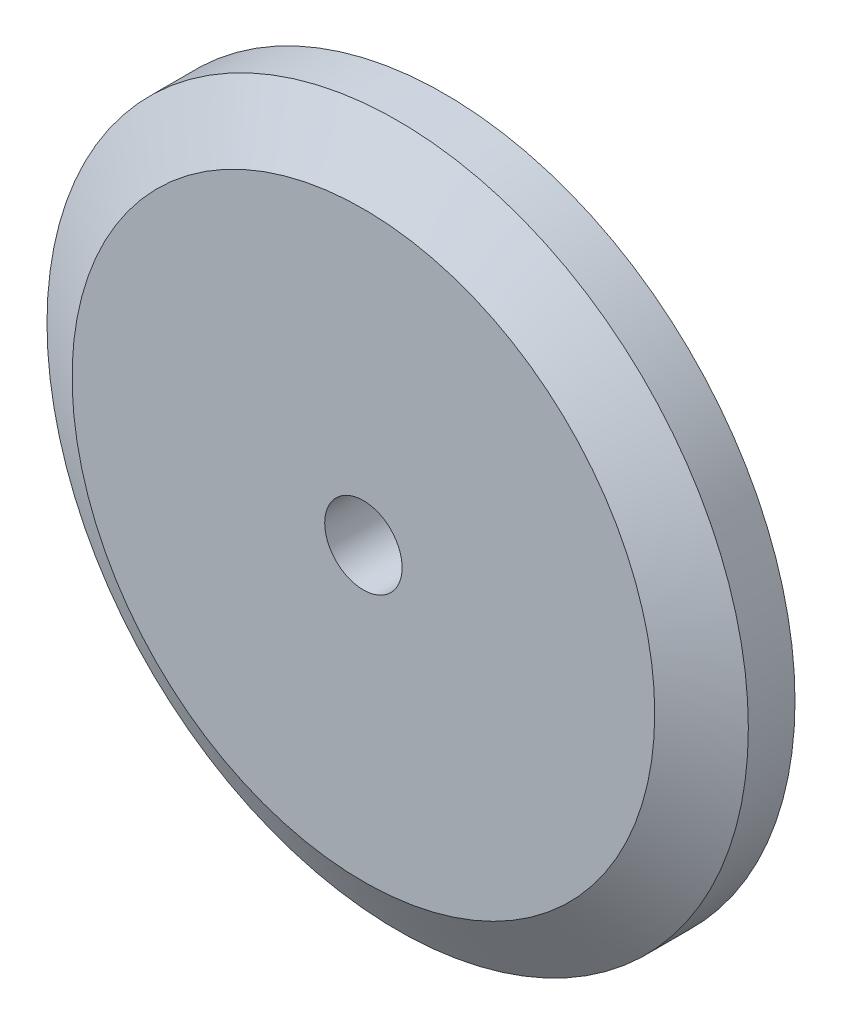
SolidWorks part; units mm, degrees
ref_plane "Front Plane" through (0, 0, 0) normal (0, 0, 1) x (1, 0, 0)
ref_plane "Top Plane" through (0, 0, 0) normal (0, 1, 0) x (1, 0, 0)
ref_plane "Right Plane" through (0, 0, 0) normal (1, 0, 0) x (0, 0, -1)
sketch "Sketch2" plane through (0, 0, -0.5) normal (0, 0, 1) x (1, 0, 0)
  circle A0 centre (40.4, -23.75) radius 5.5
  circle A1 centre (40.4, -23.75) radius 3.873 construction
  circle A2 centre (40.4, -23.75) radius 3.873 construction
  circle A3 centre (40.4, -23.75) radius 3.923
  circle A4 centre (40.4, -23.75) radius 5.5 construction
  dimension "D1" = 0.05
extrude "Boss-Extrude1" add sketch "Sketch2" along normal blind 0.5
sketch "Sketch3" plane through (0, 0, 0) normal (0, 0, 1) x (1, 0, 0)
  circle A0 centre (40.4, -23.75) radius 13
  circle A1 centre (40.4, -23.75) radius 13 construction
  circle A2 centre (40.4, -23.75) radius 3.923 construction
  circle A3 centre (40.4, -23.75) radius 3.923
  circle M1 centre (40.4, -23.75) radius 5.5
  circle M2 centre (40.4, -23.75) radius 3.923
extrude "Boss-Extrude2" add sketch "Sketch3" along normal blind 3 contours A0 M1 | M2 | M1 M2
sketch "Sketch4" plane through (0, 0, 0) normal (0, 0, -1) x (-1, 0, 0)
  circle A0 centre (-40.4, -23.75) radius 1.435 construction
  circle A1 centre (-40.4, -23.75) radius 1.435
extrude "Cut-Extrude1" cut sketch "Sketch4" against normal through all
chamfer "Chamfer1" distance 1.27 angle 60 1 edges at (53.4, -23.75, 3)
